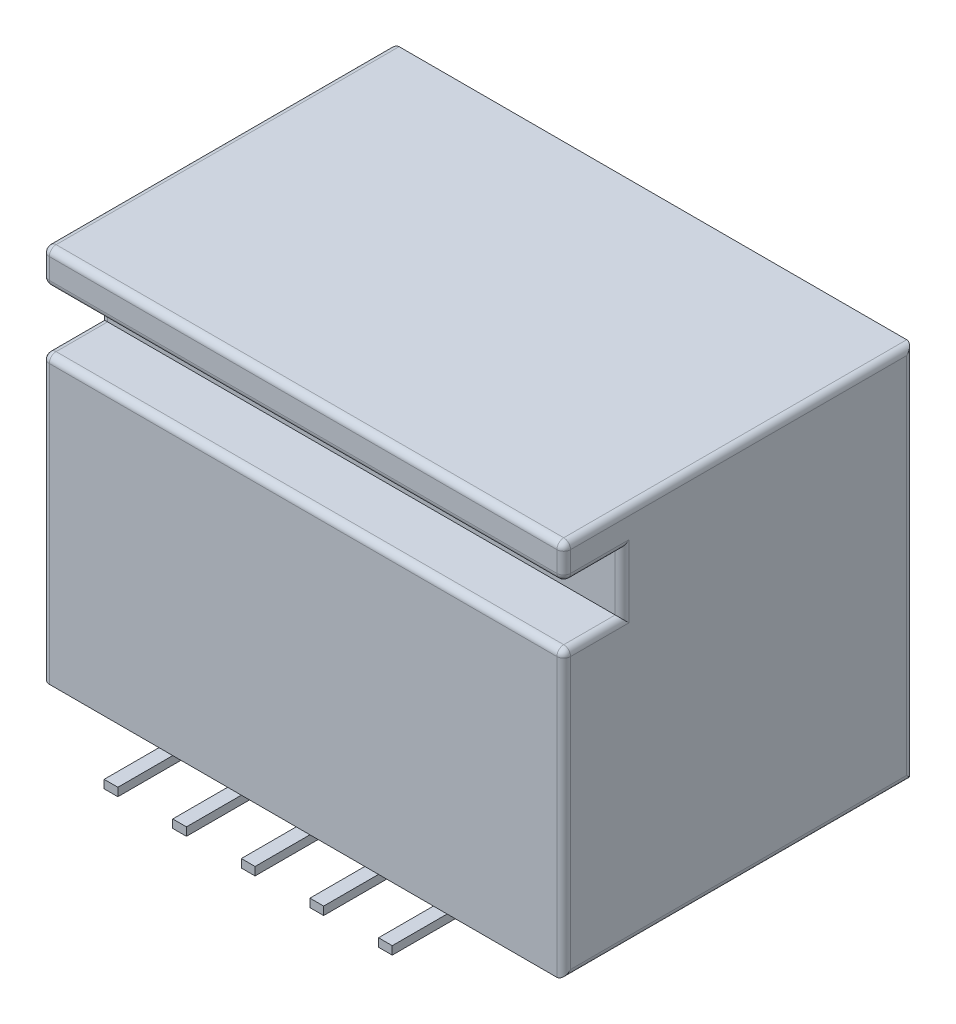
SolidWorks part; units mm, degrees
ref_plane "前视基准面" through (0, 0, 0) normal (0, 0, 1) x (1, 0, 0)
ref_plane "上视基准面" through (0, 0, 0) normal (0, 1, 0) x (1, 0, 0)
ref_plane "右视基准面" through (0, 0, 0) normal (1, 0, 0) x (0, 0, -1)
sketch "草图1" plane through (0, 0, 0) normal (1, 0, 0) x (0, 0, -1)
  line L0 (0, 0) -> (5.1, 0)
  line L1 (5.1, 0) -> (5.1, 5.5)
  line L2 (5.1, 5.5) -> (0, 5.5)
  line L7 (0, 5.5) -> (0, 5)
  line L8 (0, 5) -> (0.85, 5)
  line L9 (0.85, 5) -> (0.85, 4.15)
  line L10 (0.85, 4.15) -> (0, 4.15)
  line L11 (0, 4.15) -> (0, 0)
  dimension "D1" = 5.5
  dimension "D2" = 5.1
  dimension "D3" = 0.85
  dimension "D4" = 0.5
  dimension "D5" = 0.85
extrude "凸台-拉伸1" add sketch "草图1" along normal blind 7.6
shell "抽壳1" thickness 0.3
sketch "草图2" plane through (0, 0, 0) normal (0, -1, 0) x (1, 0, 0)
  line L0 (0, -2.55) -> (7.6, -2.55) construction
  line L1 (0, 0) -> (0, -5.1) construction
  line L2 (7.6, 0) -> (7.6, -5.1) construction
  line L3 (3.8, 0) -> (3.8, -5.1) construction
  line L4 (7.6, 0) -> (0, 0) construction
  line L5 (7.6, -5.1) -> (0, -5.1) construction
  line L6 (2.7, -4.9) -> (2.9, -4.9)
  line L7 (1.7, -4.9) -> (1.9, -4.9)
  line L8 (1.7, -4.9) -> (1.7, -5.9)
  line L9 (1.7, -5.9) -> (1.9, -5.9)
  line L10 (1.9, -4.9) -> (1.9, -5.9)
  line L11 (1.7, -4.9) -> (1.9, -5.9) construction
  line L12 (1.7, -5.9) -> (1.9, -4.9) construction
  line L13 (2.7, -4.9) -> (2.7, -5.9)
  line L14 (2.9, -4.9) -> (2.9, -5.9)
  line L15 (2.7, -5.9) -> (2.9, -5.9)
  line L16 (3.7, -4.9) -> (3.9, -4.9)
  line L17 (3.7, -4.9) -> (3.7, -5.9)
  line L18 (3.9, -4.9) -> (3.9, -5.9)
  line L19 (3.7, -5.9) -> (3.9, -5.9)
  line L20 (4.7, -4.9) -> (4.9, -4.9)
  line L21 (4.7, -4.9) -> (4.7, -5.9)
  line L22 (4.9, -4.9) -> (4.9, -5.9)
  line L23 (4.7, -5.9) -> (4.9, -5.9)
  line L24 (5.7, -4.9) -> (5.9, -4.9)
  line L25 (5.7, -4.9) -> (5.7, -5.9)
  line L26 (5.9, -4.9) -> (5.9, -5.9)
  line L27 (5.7, -5.9) -> (5.9, -5.9)
  line L28 (1.7, 0.8) -> (1.9, -0.2) construction
  line L29 (1.7, -0.2) -> (1.9, 0.8) construction
  line L30 (5.7, 0.8) -> (5.9, 0.8)
  line L31 (5.9, -0.2) -> (5.9, 0.8)
  line L32 (5.7, -0.2) -> (5.7, 0.8)
  line L33 (5.7, -0.2) -> (5.9, -0.2)
  line L34 (4.7, 0.8) -> (4.9, 0.8)
  line L35 (4.9, -0.2) -> (4.9, 0.8)
  line L36 (4.7, -0.2) -> (4.7, 0.8)
  line L37 (4.7, -0.2) -> (4.9, -0.2)
  line L38 (3.7, 0.8) -> (3.9, 0.8)
  line L39 (3.9, -0.2) -> (3.9, 0.8)
  line L40 (3.7, -0.2) -> (3.7, 0.8)
  line L41 (3.7, -0.2) -> (3.9, -0.2)
  line L42 (2.7, 0.8) -> (2.9, 0.8)
  line L43 (2.9, -0.2) -> (2.9, 0.8)
  line L44 (2.7, -0.2) -> (2.7, 0.8)
  line L45 (1.9, -0.2) -> (1.9, 0.8)
  line L46 (1.7, 0.8) -> (1.9, 0.8)
  line L47 (1.7, -0.2) -> (1.7, 0.8)
  line L48 (1.7, -0.2) -> (1.9, -0.2)
  line L49 (2.7, -0.2) -> (2.9, -0.2)
  point P12 (1.8, -5.4)
  point P17 (3.8, -5.9)
  dimension "D1" = 0.2
  dimension "D2" = 0.8
  dimension "D3" = 1
  dimension "D4" = 5
extrude "凸台-拉伸2" add sketch "草图2" along normal blind 0.12
sketch "草图3" plane through (0, 0, -0.3) normal (0, 0, -1) x (-1, 0, 0)
  line L0 (-3.8, 0.3) -> (-3.8, 5.2) construction
  line L3 (-7.3, 0.3) -> (-0.3, 0.3) construction
  line L7 (-7.3, 5.2) -> (-0.3, 5.2) construction
  line L8 (-7.3, 2) -> (-0.3, 2) construction
  line L9 (-7.3, 0.3) -> (-7.3, 5.2) construction
  line L10 (-0.3, 3.85) -> (-0.3, 0.3) construction
  circle A0 centre (-5.8, 1.4) radius 0.15
  circle A1 centre (-4.8, 1.4) radius 0.15
  circle A2 centre (-3.8, 1.4) radius 0.15
  circle A3 centre (-2.8, 1.4) radius 0.15
  circle A4 centre (-1.8, 1.4) radius 0.15
  circle A5 centre (-1.8, 2.8) radius 0.15
  circle A6 centre (-2.8, 2.8) radius 0.15
  circle A7 centre (-3.8, 2.8) radius 0.15
  circle A8 centre (-4.8, 2.8) radius 0.15
  circle A9 centre (-5.8, 2.8) radius 0.15
  point P15 (0, 0)
  dimension "D1" = 0.3
  dimension "D4" = 1.4
  dimension "D3" = 1.7
  dimension "D2" = 5
extrude "凸台-拉伸3" add sketch "草图3" along normal blind 4
fillet "圆角2" radius 0.1 18 edges at (0, 2.75, -5.1) (7.6, 2.75, -5.1) (7.6, 0, -2.55) (7.6, 4.15, -0.425) (7.6, 5, -0.425) (7.6, 4.575, -0.85) (7.6, 5.25, 0) (0, 5.25, 0) (7.6, 5.5, -2.55) (0, 5.5, -2.55) (3.8, 5.5, 0) (0, 5, -0.425) (0, 4.15, -0.425) (0, 4.575, -0.85) (3.8, 5, 0) (3.8, 4.15, 0) (0, 2.075, 0) (7.6, 2.075, 0)
